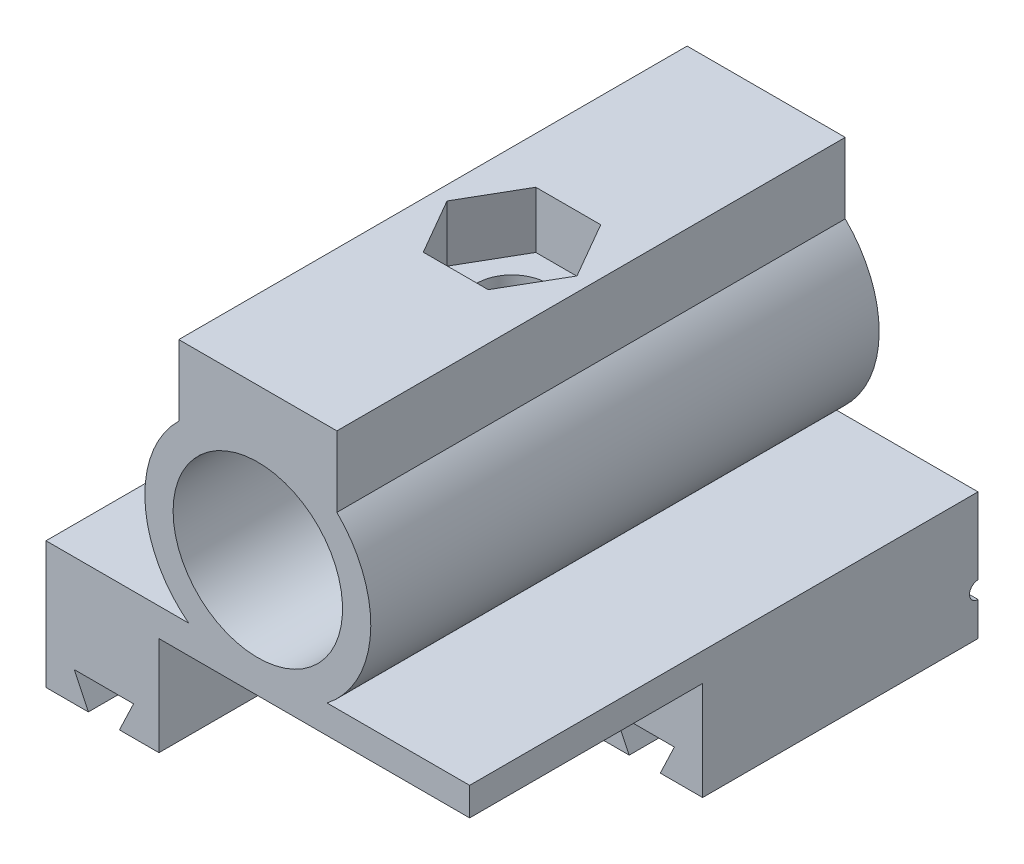
SolidWorks part; units mm, degrees
ref_plane "Front" through (0, 0, 0) normal (0, 0, 1) x (1, 0, 0)
ref_plane "Top" through (0, 0, 0) normal (0, 1, 0) x (1, 0, 0)
ref_plane "Right" through (0, 0, 0) normal (1, 0, 0) x (0, 0, -1)
sketch "Sketch1" plane through (0, 0, 0) normal (0, 1, 0) x (1, 0, 0)
  line L1 (-15, 18) -> (15, 18)
  line L2 (-15, 18) -> (-15, -18)
  line L3 (-15, -18) -> (15, -18)
  line L4 (15, 18) -> (15, -18)
  line L5 (-15, 18) -> (15, -18) construction
  line L6 (-15, -18) -> (15, 18) construction
  point P0 (0, 0)
  dimension "D1" = 30
  dimension "D2" = 36
extrude "Boss-Extrude1" add sketch "Sketch1" along normal blind 9
sketch "Sketch2" plane through (0, 0, 18) normal (0, 0, 1) x (1, 0, 0)
  line L0 (-12, 0) -> (-13, 2.1)
  line L1 (-15, 0) -> (15, 0) construction
  line L2 (-13, 2.1) -> (-8.8, 2.1)
  line L3 (-12, 0) -> (-9.8, 0)
  line L4 (-10.9, 0) -> (-10.9, 5.5217) construction
  line L5 (-9.8, 0) -> (-8.8, 2.1)
  line L6 (0, 4.653) -> (0, -4.9532) construction
  line L7 (12, 0) -> (13, 2.1)
  line L8 (13, 2.1) -> (8.8, 2.1)
  line L9 (9.8, 0) -> (8.8, 2.1)
  line L10 (12, 0) -> (9.8, 0)
  point P10 (-10.9, 2.1)
  dimension "D1" = 3
  dimension "D2" = 2.1
  dimension "D3" = 2.1
  dimension "D4" = 1.1
extrude "Cut-Extrude1" cut sketch "Sketch2" against normal through all
sketch "Sketch3" plane through (0, 0, 18) normal (0, 0, 1) x (1, 0, 0)
  line L1 (15, 0) -> (-7, 0)
  line L2 (15, 0) -> (15, 7)
  line L3 (15, 7) -> (-7, 7)
  line L4 (-7, 0) -> (-7, 7)
  dimension "D1" = 7
  dimension "D2" = 22
extrude "Cut-Extrude2" cut sketch "Sketch3" against normal blind 16.5
sketch "Sketch4" plane through (0, 0, 1.5) normal (0, 0, 1) x (1, 0, 0)
  line L0 (-7, 0) -> (9.8, 0) construction
  line L1 (-7, 7) -> (7, 7)
  line L2 (-7, 7) -> (-7, 0)
  line L3 (-7, 0) -> (7, 0)
  line L4 (7, 7) -> (7, 0)
  dimension "D1" = 14
extrude "Cut-Extrude3" cut sketch "Sketch4" against normal through all
sketch "Sketch5" plane through (0, 0, 18) normal (0, 0, 1) x (1, 0, 0)
  line L0 (-15, 9) -> (15, 9) construction
  line L1 (-4.899, 9) -> (4.899, 9)
  line L3 (-5.5988, 26.0388) -> (5.5988, 26.0388)
  line L4 (-5.5988, 26.0388) -> (-5.5988, 21.0388)
  line L6 (5.5988, 26.0388) -> (5.5988, 21.0388)
  arc A1 (4.899, 9) -> (5.5988, 21.0388) centre (0, 15.3246) ccw
  arc A2 (-5.5988, 21.0388) -> (-4.899, 9) centre (0, 15.3246) ccw
  point P4 (0, 21)
  dimension "D1" = 5
  dimension "D2" = 8
extrude "Boss-Extrude4" add sketch "Sketch5" against normal up to surface (36 mm away) contours L6 A1 L1 A2 L4 L3 up to face at (0, 2.525, -18)
sketch "Sketch6" plane through (0, 0, -18) normal (0, 0, -1) x (-1, 0, 0)
  circle A0 centre (0, 15.3246) radius 6
  dimension "D1" = 12
extrude "Cut-Extrude4" cut sketch "Sketch6" against normal through all
sketch "Sketch7" plane through (0, 26.0388, 0) normal (0, 1, 0) x (1, 0, 0)
  line L1 (2.3, -3.9837) -> (4.6, 0)
  line L2 (4.6, 0) -> (2.3, 3.9837)
  line L3 (2.3, 3.9837) -> (-2.3, 3.9837)
  line L4 (-2.3, 3.9837) -> (-4.6, 0)
  line L5 (-4.6, 0) -> (-2.3, -3.9837)
  line L6 (-2.3, -3.9837) -> (2.3, -3.9837)
  circle A0 centre (0, 0) radius 3.9837 construction
  dimension "D1" = 4.6
extrude "Cut-Extrude8" cut sketch "Sketch7" against normal blind 4
sketch "Sketch8" plane through (0, 22.0388, 0) normal (0, 1, 0) x (1, 0, 0)
  circle A0 centre (0, 0) radius 2.5
extrude "Cut-Extrude9" cut sketch "Sketch8" against normal blind 3
sketch "Sketch9" plane through (-15, 0, 0) normal (-1, 0, 0) x (0, 0, 1)
  line L0 (-18, 9) -> (-18, 0) construction
  line L1 (-18, 0) -> (18, 0) construction
  circle A0 centre (-18, 3) radius 0.6
  dimension "D1" = 3
  dimension "D2" = 1.2
extrude "Cut-Extrude10" cut sketch "Sketch9" against normal through all
